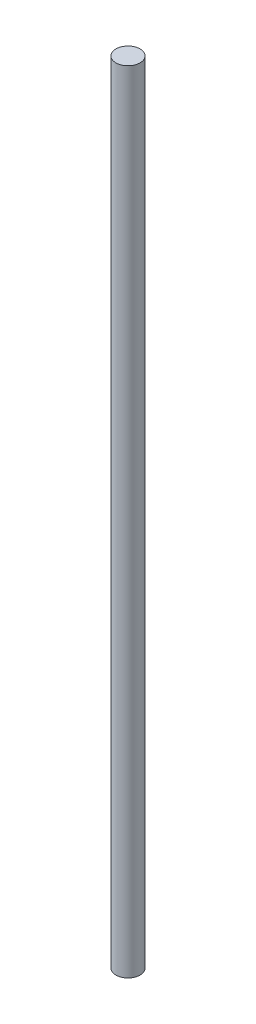
SolidWorks part; units mm, degrees
ref_plane "Front Plane" through (0, 0, 0) normal (0, 0, 1) x (1, 0, 0)
ref_plane "Top Plane" through (0, 0, 0) normal (0, 1, 0) x (1, 0, 0)
ref_plane "Right Plane" through (0, 0, 0) normal (1, 0, 0) x (0, 0, -1)
sketch "Sketch1" plane through (0, 0, 0) normal (0, 1, 0) x (1, 0, 0)
  circle A0 centre (0, 0) radius 3
  dimension "D1" = 6
extrude "Boss-Extrude1" add sketch "Sketch1" along normal blind 196
